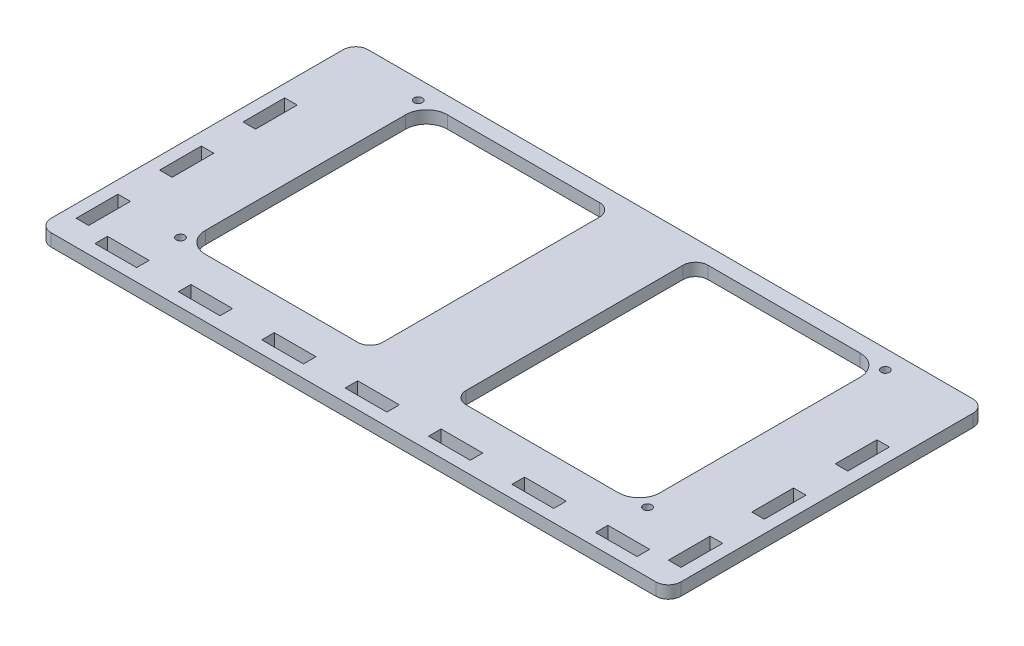
SolidWorks part; units mm, degrees
material "Maple"
ref_plane "Front Plane" through (0, 0, 0) normal (0, 0, 1) x (1, 0, 0)
ref_plane "Top Plane" through (0, 0, 0) normal (0, 1, 0) x (1, 0, 0)
ref_plane "Right Plane" through (0, 0, 0) normal (1, 0, 0) x (0, 0, -1)
sketch "Sketch1" plane through (0, 0, 0) normal (0, 1, 0) x (1, 0, 0)
  line L1 (0, 0) -> (121, 0)
  line L2 (0, 0) -> (0, -66)
  line L3 (0, -66) -> (121, -66)
  line L4 (121, 0) -> (121, -66)
  dimension "D1" = 121
  dimension "D2" = 66
extrude "Boss-Extrude1" add sketch "Sketch1" along normal blind 3
sketch "Sketch2" plane through (0, 3, 0) normal (0, 1, 0) x (1, 0, 0)
  line L0 (60.5, -66) -> (60.5, 0) construction
  line L2 (6, -4) -> (115, -4)
  line L3 (6, -4) -> (6, -62)
  line L4 (6, -62) -> (115, -62)
  line L5 (115, -4) -> (115, -62)
  line L6 (6, -4) -> (115, -62) construction
  line L7 (6, -62) -> (115, -4) construction
  line L9 (0, -66) -> (121, -66) construction
  line L10 (121, 0) -> (0, 0) construction
  line L11 (0, -33) -> (121, -33) construction
  line L12 (0, 0) -> (0, -66) construction
  line L13 (121, -66) -> (121, 0) construction
  point P4 (60.5, -33)
  dimension "D1" = 29
  dimension "D2" = 54.5
  dimension "D3" = 58
  dimension "D4" = 109
extrude "Cut-Extrude1" cut sketch "Sketch2" against normal through all
fillet "Fillet1" radius 5 4 edges at (6, 1.5, 62) (115, 1.5, 62) (115, 1.5, 4) (6, 1.5, 4)
sketch "Sketch3" plane through (0, 3, 0) normal (0, 1, 0) x (1, 0, 0)
  line L0 (60.5, 0) -> (60.5, -66) construction
  line L1 (121, 0) -> (0, 0) construction
  line L2 (0, -66) -> (121, -66) construction
  line L3 (11, -62) -> (110, -62) construction
  line L4 (50.5, -4) -> (70.5, -4)
  line L5 (50.5, -4) -> (50.5, -62)
  line L6 (50.5, -62) -> (70.5, -62)
  line L7 (70.5, -4) -> (70.5, -62)
  line L8 (50.5, -4) -> (70.5, -62) construction
  line L9 (50.5, -62) -> (70.5, -4) construction
  point P6 (60.5, -33)
  dimension "D1" = 20
extrude "Boss-Extrude2" add sketch "Sketch3" against normal through all
fillet "Fillet2" radius 3 4 edges at (70.5, 1.5, 62) (70.5, 1.5, 4) (50.5, 1.5, 62) (50.5, 1.5, 4)
sketch "Sketch4" plane through (0, 3, 0) normal (0, 1, 0) x (1, 0, 0)
  line L0 (60.5, -66) -> (60.5, 0) construction
  line L1 (121, -66) -> (121, 0) construction
  line L2 (0, -66) -> (121, -66) construction
  line L3 (121, 0) -> (0, 0) construction
  line L4 (0, 0) -> (0, -66) construction
  line L5 (0, -33) -> (121, -33) construction
  circle A0 centre (116.5, -61.5) radius 1
  circle A1 centre (116.5, -4.5) radius 1
  circle A2 centre (4.5, -4.5) radius 1
  circle A3 centre (4.5, -61.5) radius 1
  dimension "D1" = 2
  dimension "D6" = 2
  dimension "D7" = 2
  dimension "D10" = 2
  dimension "D3" = 28.5
  dimension "D2" = 56
  dimension "D5" = 28.5
  dimension "D4" = 56
  dimension "D11" = 28.5
  dimension "D8" = 28.5
  dimension "D9" = 56
  dimension "D12" = 56
extrude "Cut-Extrude2" cut sketch "Sketch4" against normal through all
sketch "Sketch5" plane through (0, 3, 0) normal (0, 1, 0) x (1, 0, 0)
  line L0 (121, 0) -> (0, 0) construction
  line L1 (-15, 0) -> (136, 0)
  line L2 (-15, 0) -> (-15, -76)
  line L3 (-15, -76) -> (136, -76)
  line L4 (136, 0) -> (136, -76)
  line L5 (0, 0) -> (0, -66) construction
  line L6 (121, -66) -> (121, 0) construction
  line L7 (0, -66) -> (121, -66) construction
  line L8 (0, 0) -> (0, -66)
  line L9 (0, -66) -> (121, -66)
  line L10 (121, -66) -> (121, 0)
  line M25 (0, 0) -> (0, -66)
  line M26 (0, -66) -> (121, -66)
  line M27 (121, -66) -> (121, 0)
  dimension "D1" = 15
  dimension "D2" = 15
  dimension "D3" = 10
extrude "Boss-Extrude3" add sketch "Sketch5" against normal through all contours L4 L1 L2 L3 M27 M26 M25
fillet "Fillet3" radius 3 4 edges at (-15, 1.5, 0) (-15, 1.5, 76) (136, 1.5, 76) (136, 1.5, 0)
sketch "Sketch6" plane through (0, 0, 0) normal (0, -1, 0) x (1, 0, 0)
  line L1 (133, 20) -> (130, 20)
  line L2 (133, 20) -> (133, 30)
  line L3 (133, 30) -> (130, 30)
  line L4 (130, 20) -> (130, 30)
  line L5 (133, 40) -> (130, 40)
  line L6 (133, 40) -> (133, 50)
  line L7 (133, 50) -> (130, 50)
  line L8 (130, 40) -> (130, 50)
  line L9 (133, 60) -> (130, 60)
  line L10 (133, 60) -> (133, 70)
  line L11 (133, 70) -> (130, 70)
  line L12 (130, 60) -> (130, 70)
  line L13 (125.5, 70) -> (115.5, 70)
  line L14 (125.5, 70) -> (125.5, 73)
  line L15 (125.5, 73) -> (115.5, 73)
  line L16 (115.5, 70) -> (115.5, 73)
  line L17 (105.5, 70) -> (95.5, 70)
  line L18 (105.5, 70) -> (105.5, 73)
  line L19 (105.5, 73) -> (95.5, 73)
  line L20 (95.5, 70) -> (95.5, 73)
  line L21 (85.5, 70) -> (75.5, 70)
  line L22 (85.5, 70) -> (85.5, 73)
  line L23 (85.5, 73) -> (75.5, 73)
  line L24 (75.5, 70) -> (75.5, 73)
  line L25 (65.5, 70) -> (55.5, 70)
  line L26 (65.5, 70) -> (65.5, 73)
  line L27 (65.5, 73) -> (55.5, 73)
  line L28 (55.5, 70) -> (55.5, 73)
  line L29 (45.5, 70) -> (35.5, 70)
  line L30 (45.5, 70) -> (45.5, 73)
  line L31 (45.5, 73) -> (35.5, 73)
  line L32 (35.5, 70) -> (35.5, 73)
  line L33 (25.5, 70) -> (15.5, 70)
  line L34 (25.5, 70) -> (25.5, 73)
  line L35 (25.5, 73) -> (15.5, 73)
  line L36 (15.5, 70) -> (15.5, 73)
  line L37 (5.5, 70) -> (-4.5, 70)
  line L38 (5.5, 70) -> (5.5, 73)
  line L39 (5.5, 73) -> (-4.5, 73)
  line L40 (-4.5, 70) -> (-4.5, 73)
  line L41 (-9, 60) -> (-12, 60)
  line L42 (-9, 60) -> (-9, 70)
  line L43 (-9, 70) -> (-12, 70)
  line L44 (-12, 60) -> (-12, 70)
  line L45 (-9, 40) -> (-12, 40)
  line L46 (-9, 40) -> (-9, 50)
  line L47 (-9, 50) -> (-12, 50)
  line L48 (-12, 40) -> (-12, 50)
  line L49 (-9, 20) -> (-12, 20)
  line L50 (-9, 20) -> (-9, 30)
  line L51 (-9, 30) -> (-12, 30)
  line L52 (-12, 20) -> (-12, 30)
extrude "Cut-Extrude3" cut sketch "Sketch6" against normal through all
equation "\"D6@Sketch4\"=\"D1@Sketch4\""
equation "\"D7@Sketch4\"=\"D6@Sketch4\""
equation "\"D10@Sketch4\"=\"D7@Sketch4\""
equation "\"D5@Sketch4\"=\"D3@Sketch4\""
equation "\"D4@Sketch4\"=\"D2@Sketch4\""
equation "\"D11@Sketch4\"=\"D3@Sketch4\""
equation "\"D8@Sketch4\"=\"D11@Sketch4\""
equation "\"D9@Sketch4\"=\"D2@Sketch4\""
equation "\"D12@Sketch4\"=\"D9@Sketch4\""
